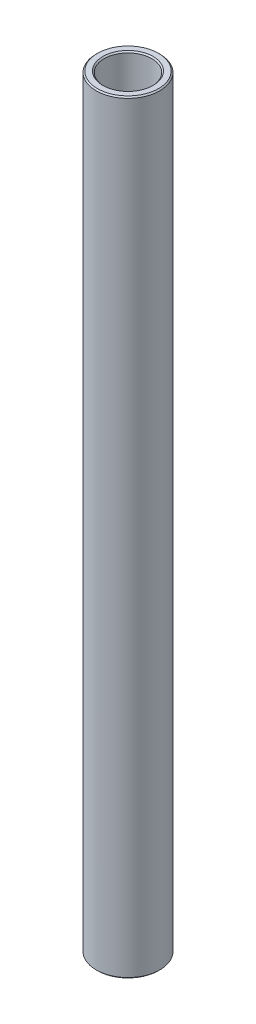
SolidWorks part; units mm, degrees
ref_plane "Front Plane" through (0, 0, 0) normal (0, 0, 1) x (1, 0, 0)
ref_plane "Top Plane" through (0, 0, 0) normal (0, 1, 0) x (1, 0, 0)
ref_plane "Right Plane" through (0, 0, 0) normal (1, 0, 0) x (0, 0, -1)
sketch "Sketch1" plane through (0, 0, 0) normal (0, 0, 1) x (1, 0, 0)
  line L0 (0, 11.6086) -> (0, -11.6086) construction
  line L1 (4.7625, 76.2) -> (6.35, 76.2)
  line L2 (6.35, 76.2) -> (6.35, -76.2)
  line L3 (6.35, -76.2) -> (4.7625, -76.2)
  line L4 (4.7625, -76.2) -> (4.7625, 76.2)
  line L5 (4.7625, 0) -> (0, 0) construction
  dimension "D1" = 9.525
  dimension "D2" = 12.7
  dimension "D3" = 152.4
revolve "Revolve1" add sketch "Sketch1" angle 360 about L0
chamfer "Chamfer1" distance 0.254 angle 45 4 edges at (-4.7625, -76.2, 0) (-6.35, -76.2, 0) (-6.35, 76.2, 0) (-4.7625, 76.2, 0)
